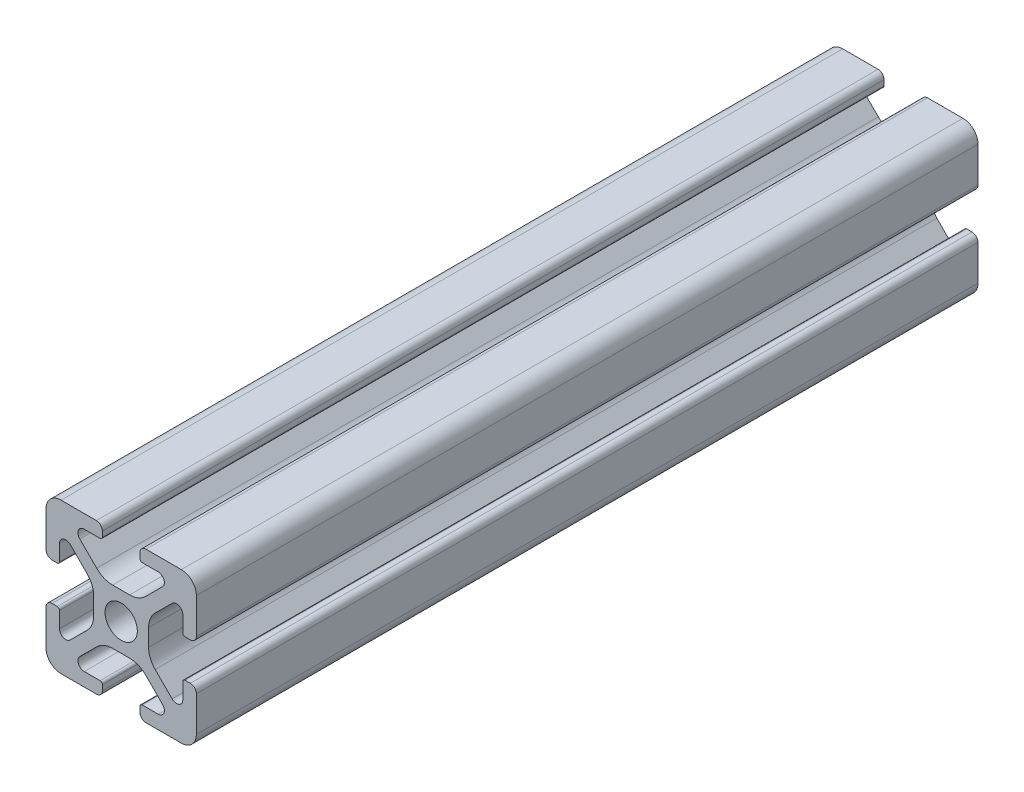
SolidWorks part; units mm, degrees
ref_plane "Ebene vorne" through (0, 0, 0) normal (0, 0, 1) x (1, 0, 0)
ref_plane "Ebene oben" through (0, 0, 0) normal (0, 1, 0) x (1, 0, 0)
ref_plane "Ebene rechts" through (0, 0, 0) normal (1, 0, 0) x (0, 0, -1)
ref_plane "Ebene1" through (0, 0, 100) normal (0, 0, 1) x (1, 0, 0)
sketch "Skizze1" plane through (0, 0, 100) normal (0, 0, 1) x (1, 0, 0)
  line L0 (12.5, 1.5) -> (12.5, 0.8)
  line L1 (13.3, 0) -> (18, 0)
  line L2 (20, 2) -> (20, 6.7)
  line L3 (19.2, 7.5) -> (18.5, 7.5)
  line L4 (18.2, 7.2) -> (18.2, 5.0824)
  line L5 (16.779, 4.4938) -> (14.5287, 6.7441)
  line L6 (13.65, 8.8654) -> (13.65, 11.1346)
  line L7 (14.5287, 13.2559) -> (16.779, 15.5062)
  line L8 (18.2, 14.9176) -> (18.2, 12.8)
  line L9 (18.5, 12.5) -> (19.2, 12.5)
  line L10 (20, 13.3) -> (20, 18)
  line L11 (18, 20) -> (13.3, 20)
  line L12 (12.5, 19.2) -> (12.5, 18.5)
  line L13 (12.8, 18.2) -> (14.9176, 18.2)
  line L14 (15.5062, 16.779) -> (13.2559, 14.5287)
  line L15 (11.1346, 13.65) -> (8.8654, 13.65)
  line L16 (6.7441, 14.5287) -> (4.4938, 16.779)
  line L17 (5.0824, 18.2) -> (7.2, 18.2)
  line L18 (7.5, 18.5) -> (7.5, 19.2)
  line L19 (6.7, 20) -> (2, 20)
  line L20 (0, 18) -> (0, 13.3)
  line L21 (0.8, 12.5) -> (1.5, 12.5)
  line L22 (1.8, 12.8) -> (1.8, 14.9176)
  line L23 (3.221, 15.5062) -> (5.4713, 13.2559)
  line L24 (6.35, 11.1346) -> (6.35, 8.8654)
  line L25 (5.4713, 6.7441) -> (3.221, 4.4938)
  line L26 (1.8, 5.0824) -> (1.8, 7.2)
  line L27 (1.5, 7.5) -> (0.8, 7.5)
  line L28 (0, 6.7) -> (0, 2)
  line L29 (2, 0) -> (6.7, 0)
  line L30 (7.5, 0.8) -> (7.5, 1.5)
  line L31 (7.2, 1.8) -> (5.0824, 1.8)
  line L32 (4.4938, 3.221) -> (6.7441, 5.4713)
  line L33 (8.8654, 6.35) -> (11.1346, 6.35)
  line L34 (13.2559, 5.4713) -> (15.5062, 3.221)
  line L35 (14.9176, 1.8) -> (12.8, 1.8)
  circle A0 centre (10, 10) radius 2.15
  arc A1 (12.8, 1.8) -> (12.5, 1.5) centre (12.8, 1.5) ccw
  arc A2 (12.5, 0.8) -> (13.3, 0) centre (13.3, 0.8) ccw
  arc A3 (18, 0) -> (20, 2) centre (18, 2) ccw
  arc A4 (20, 6.7) -> (19.2, 7.5) centre (19.2, 6.7) ccw
  arc A5 (18.5, 7.5) -> (18.2, 7.2) centre (18.5, 7.2) ccw
  arc A6 (18.2, 5.0824) -> (16.779, 4.4938) centre (17.3676, 5.0824) cw
  arc A7 (14.5287, 6.7441) -> (13.65, 8.8654) centre (16.65, 8.8654) cw
  arc A8 (13.65, 11.1346) -> (14.5287, 13.2559) centre (16.65, 11.1346) cw
  arc A9 (16.779, 15.5062) -> (18.2, 14.9176) centre (17.3676, 14.9176) cw
  arc A10 (18.2, 12.8) -> (18.5, 12.5) centre (18.5, 12.8) ccw
  arc A11 (19.2, 12.5) -> (20, 13.3) centre (19.2, 13.3) ccw
  arc A12 (20, 18) -> (18, 20) centre (18, 18) ccw
  arc A13 (13.3, 20) -> (12.5, 19.2) centre (13.3, 19.2) ccw
  arc A14 (12.5, 18.5) -> (12.8, 18.2) centre (12.8, 18.5) ccw
  arc A15 (14.9176, 18.2) -> (15.5062, 16.779) centre (14.9176, 17.3676) cw
  arc A16 (13.2559, 14.5287) -> (11.1346, 13.65) centre (11.1346, 16.65) cw
  arc A17 (8.8654, 13.65) -> (6.7441, 14.5287) centre (8.8654, 16.65) cw
  arc A18 (4.4938, 16.779) -> (5.0824, 18.2) centre (5.0824, 17.3676) cw
  arc A19 (7.2, 18.2) -> (7.5, 18.5) centre (7.2, 18.5) ccw
  arc A20 (7.5, 19.2) -> (6.7, 20) centre (6.7, 19.2) ccw
  arc A21 (2, 20) -> (0, 18) centre (2, 18) ccw
  arc A22 (0, 13.3) -> (0.8, 12.5) centre (0.8, 13.3) ccw
  arc A23 (1.5, 12.5) -> (1.8, 12.8) centre (1.5, 12.8) ccw
  arc A24 (1.8, 14.9176) -> (3.221, 15.5062) centre (2.6324, 14.9176) cw
  arc A25 (5.4713, 13.2559) -> (6.35, 11.1346) centre (3.35, 11.1346) cw
  arc A26 (6.35, 8.8654) -> (5.4713, 6.7441) centre (3.35, 8.8654) cw
  arc A27 (3.221, 4.4938) -> (1.8, 5.0824) centre (2.6324, 5.0824) cw
  arc A28 (1.8, 7.2) -> (1.5, 7.5) centre (1.5, 7.2) ccw
  arc A29 (0.8, 7.5) -> (0, 6.7) centre (0.8, 6.7) ccw
  arc A30 (0, 2) -> (2, 0) centre (2, 2) ccw
  arc A31 (6.7, 0) -> (7.5, 0.8) centre (6.7, 0.8) ccw
  arc A32 (7.5, 1.5) -> (7.2, 1.8) centre (7.2, 1.5) ccw
  arc A33 (5.0824, 1.8) -> (4.4938, 3.221) centre (5.0824, 2.6324) cw
  arc A34 (6.7441, 5.4713) -> (8.8654, 6.35) centre (8.8654, 3.35) cw
  arc A35 (11.1346, 6.35) -> (13.2559, 5.4713) centre (11.1346, 3.35) cw
  arc A36 (15.5062, 3.221) -> (14.9176, 1.8) centre (14.9176, 2.6324) cw
extrude "Aufsatz-Linear austragen1" add sketch "Skizze1" against normal blind 104
